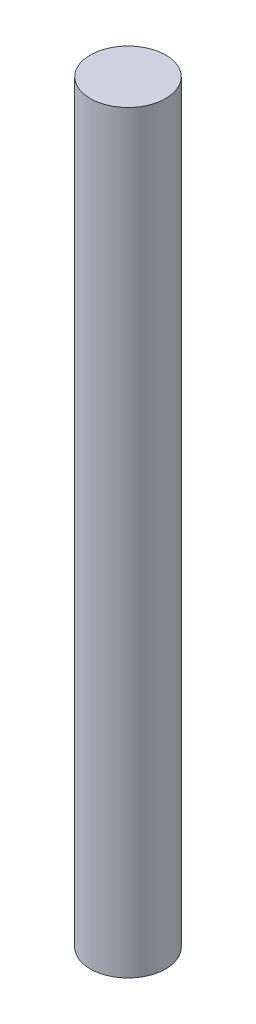
SolidWorks part; units mm, degrees
ref_plane "Front Plane" through (0, 0, 0) normal (0, 0, 1) x (1, 0, 0)
ref_plane "Top Plane" through (0, 0, 0) normal (0, 1, 0) x (1, 0, 0)
ref_plane "Right Plane" through (0, 0, 0) normal (1, 0, 0) x (0, 0, -1)
sketch "Sketch2" plane through (0, 0, 0) normal (0, 1, 0) x (1, 0, 0)
  circle A0 centre (0, 0) radius 0.1
  dimension "D1" = 0.2
extrude "Boss-Extrude2" add sketch "Sketch2" along normal blind 2
